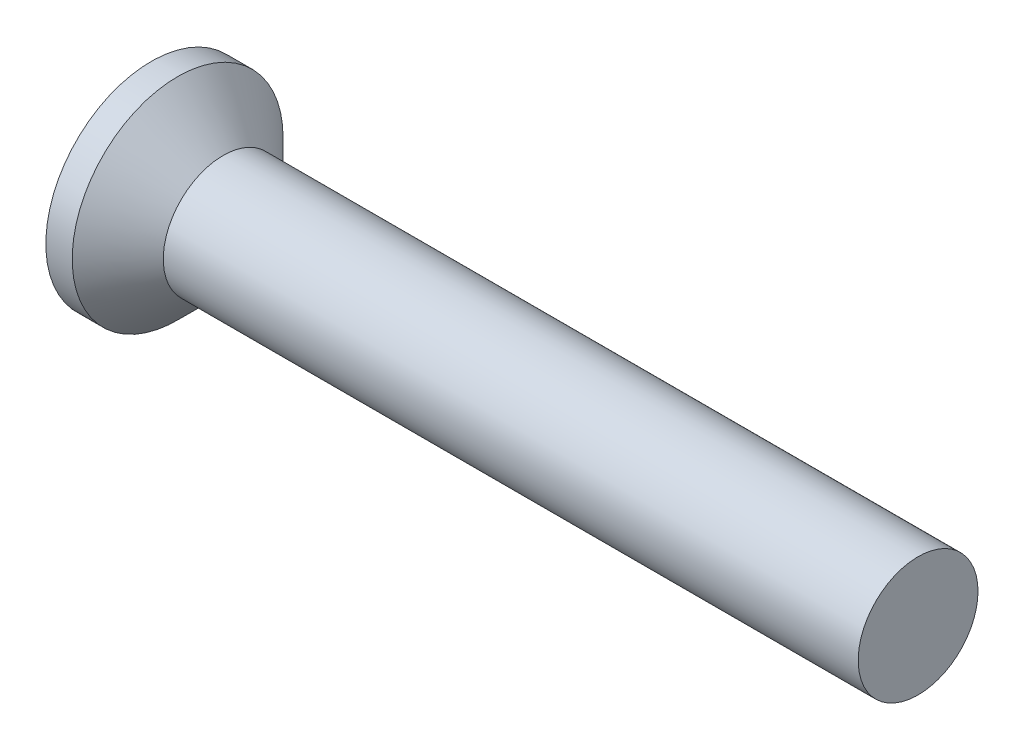
SolidWorks part; units mm, degrees
ref_plane "Front" through (0, 0, 0) normal (0, 0, 1) x (1, 0, 0)
ref_plane "Top" through (0, 0, 0) normal (0, 1, 0) x (1, 0, 0)
ref_plane "Right" through (0, 0, 0) normal (1, 0, 0) x (0, 0, -1)
sketch "Sketch1" plane through (0, 0, 0) normal (0, 0, 1) x (1, 0, 0)
  line L0 (16, 1.25) -> (2.4, 1.25)
  line L1 (2.4, 1.25) -> (1.5, 1.25)
  line L2 (1.5, 1.25) -> (0.55, 2.2)
  line L3 (0.55, 2.2) -> (0, 2.2)
  line L4 (16, 1.25) -> (16, 0)
  line L5 (4.5158, 0) -> (-89.8219, 0) construction
  line L6 (16, 0) -> (0, 0)
  line L7 (0, 2.2) -> (0, 0)
  dimension "d" = 2.5
  dimension "D1" = 45
  dimension "dk" = 4.4
  dimension "k" = 1.5
  dimension "l" = 16
  dimension "a" = 0.9
revolve "Base" add sketch "Sketch1" angle 360 about L5
cosmetic thread "ThreadCosmetic1" [suppressed] parameters "bb"=14.5, "THD_MINOR"=2.013
sketch "Sketch6" plane through (0, 0, 0) normal (1, 0, 0) x (0, 0, -1)
  line L0 (-1.9271, 0) -> (2.0512, 0) construction
  line L1 (0, 1.8651) -> (0, -2.0207) construction
  line L2 (0.29, 0.29) -> (0.29, 1.45)
  line L3 (0.29, 1.45) -> (-0.29, 1.45)
  line L4 (-0.29, 0.29) -> (-0.29, 1.45)
  line L5 (0.29, 0.29) -> (1.45, 0.29)
  line L6 (1.45, 0.29) -> (1.45, -0.29)
  line L7 (-1.45, 0.29) -> (-1.45, -0.29)
  line L8 (-0.29, 0.29) -> (-1.45, 0.29)
  line L9 (-0.29, -0.29) -> (-1.45, -0.29)
  line L10 (0.29, -0.29) -> (1.45, -0.29)
  line L11 (-0.29, -0.29) -> (-0.29, -1.45)
  line L12 (0.29, -1.45) -> (-0.29, -1.45)
  line L13 (0.29, -0.29) -> (0.29, -1.45)
  point P16 (-1.45, 0)
  point P17 (1.45, 0)
extrude "CrossRecess" cut sketch "Sketch6" along normal blind 0.75
draft "Draft9" type of draft neutral plane draft angle 30 faces to draft 4 face at (0.375, -1.45, 0) face at (0.375, 0, 1.45) face at (0.375, 0, -1.45) face at (0.375, 1.45, 0) neutral plane through (0, 2.2, 0) neutral plane normal (-1, 0, 0) parameters "D1"=30
fillet "Fillet5" radius 0.3 4 edges at (0.375, -0.29, -0.29) (0.375, -0.29, 0.29) (0.375, 0.29, -0.29) (0.375, 0.29, 0.29)
sketch "Sketch7" plane through (0, 0, 0) normal (1, 0, 0) x (0, 0, -1)
  line L0 (-2.0126, 0) -> (1.9757, 0) construction
  line L1 (0, 1.9314) -> (0, -2.0126) construction
  line L2 (0, 0) -> (1.5555, 1.5555) construction
  line L3 (0, 0.4333) -> (1.0253, 1.0253)
  line L4 (-1.5402, 1.5402) -> (0, 0) construction
  line L5 (0.4333, 0) -> (1.0253, 1.0253)
  line L6 (0, -0.4333) -> (1.0253, -1.0253)
  line L7 (0.4333, 0) -> (1.0253, -1.0253)
  line L8 (-0.4333, 0) -> (-1.0253, -1.0253)
  line L9 (0, -0.4333) -> (-1.0253, -1.0253)
  line L10 (-0.4333, 0) -> (-1.0253, 1.0253)
  line L11 (0, 0.4333) -> (-1.0253, 1.0253)
  dimension "D3" = 15
  dimension "m" = 2.9
extrude "Cut-Extrude3" [suppressed] cut sketch "Sketch7" along normal blind 10 draft 20
sketch "Sketch10" plane through (0, 0, 0) normal (0, 0, 1) x (1, 0, 0)
  line L0 (62.2289, 0) -> (-1.9277, 0) construction
  line L1 (1.5, 1.25) -> (1.95, 1.25)
  line L4 (1.95, 1.25) -> (1.95, 0)
  line L7 (1.95, 0) -> (1.5, 0)
  line L9 (1.5, 1.25) -> (0.55, 2.2) construction
  line L10 (1.5, 1.25) -> (1.5, 0)
  dimension "p" = 0.45
revolve "Revolve2" add sketch "Sketch10" angle 360 about L0
sketch "Sketch8" plane through (0, 0, 0) normal (0, 0, 1) x (1, 0, 0)
  line L0 (-9, 1.25) -> (-10.1, 1.0065)
  line L1 (-10.1, 1.0065) -> (5, 1.0065)
  line L3 (16, -1.25) -> (16, 1.25) construction
  line L6 (5, 1.0065) -> (5, 6.0065)
  line L7 (5, 6.0065) -> (-9, 6.0065)
  line L8 (-9, 6.0065) -> (-9, 1.25)
  line L9 (62.4753, 0) -> (52.9594, 0) construction
  dimension "D1" = 5
  dimension "x" = 1.1
  dimension "d" = 2.5
  dimension "THD_MINOR" = 2.013
  dimension "b" = 25
sketch "Sketch11" plane through (0, 0, 0) normal (0, 0, 1) x (1, 0, 0)
  line L0 (16, 1.0391) -> (16.1218, 1.25)
  line L1 (16.1218, 1.25) -> (16.1218, 1.4935)
  line L2 (16.1218, 1.4935) -> (15.8782, 1.4935)
  line L3 (15.8782, 1.4935) -> (15.8782, 1.25)
  line L4 (15.8782, 1.25) -> (16, 1.0391)
  line L5 (16, -1.25) -> (16, 1.25) construction
  line L6 (0, 0) -> (66.0064, 0) construction
  dimension "D1" = 2.5
  dimension "D2" = 0.2435
revolve "Cut-Revolve10" [suppressed] cut sketch "Sketch11" angle 360 about L6
pattern_linear "LPattern10" [suppressed] count 50 spacing 0.2922 along (1, 0, 0)
equation "\"D1@Sketch6\" = \"m@Sketch6\" / 5"
equation "\"D1@CrossRecess\" = \"k@Sketch1\" / 2"
equation "\"D1@Sketch11\" = \"d@Sketch1\""
equation "\"D2@Sketch11\" =  ( \"d@Sketch1\" - \"THD_MINOR@ThreadCosmetic1\" )  / 2"
equation "\"D3@LPattern10\" = \"D2@Sketch11\" * 1.2"
equation "\"D1@LPattern10\" = \"bb@ThreadCosmetic1\" / \"D3@LPattern10\" "
